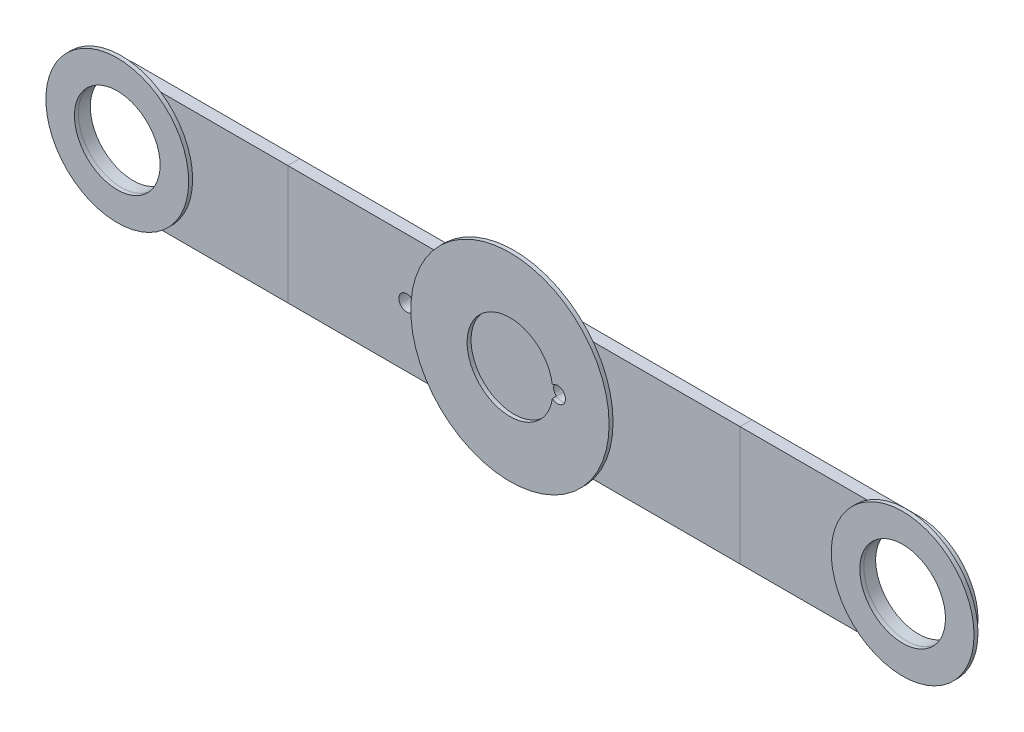
SolidWorks part; units mm, degrees
ref_plane "Front Plane" through (0, 0, 0) normal (0, 0, 1) x (1, 0, 0)
ref_plane "Top Plane" through (0, 0, 0) normal (0, 1, 0) x (1, 0, 0)
ref_plane "Right Plane" through (0, 0, 0) normal (1, 0, 0) x (0, 0, -1)
sketch "Sketch1" plane through (0, 0, 0) normal (0, 0, 1) x (1, 0, 0)
  line L0 (28.5, 7.5) -> (49.5, 7.5)
  line L1 (-28.5, -7.5) -> (28.5, -7.5)
  line L2 (-28.5, -7.5) -> (-28.5, 7.5)
  line L3 (-28.5, 7.5) -> (28.5, 7.5)
  line L4 (28.5, -7.5) -> (28.5, 7.5)
  line L5 (-28.5, -7.5) -> (28.5, 7.5) construction
  line L6 (-28.5, 7.5) -> (28.5, -7.5) construction
  line L7 (-49.5, -7.5) -> (-28.5, -7.5)
  line L8 (49.5, -7.5) -> (28.5, -7.5)
  line L9 (0, 7.5) -> (0, -7.5) construction
  line L10 (-28.5, 0) -> (28.5, 0) construction
  line L11 (-28.5, 7.5) -> (-49.5, 7.5)
  arc A0 (49.5, -7.5) -> (49.5, 7.5) centre (49.5, 0) ccw
  circle A1 centre (-49.5, 0) radius 5.4
  circle A2 centre (49.5, 0) radius 5.4
  arc A3 (-49.5, -7.5) -> (-49.5, 7.5) centre (-49.5, 0) cw
  point P0 (0, 0)
  point P18 (0, 0)
  dimension "D3" = 57
  dimension "D8" = 10.8
  dimension "D1" = 15
  dimension "D2" = 57
extrude "Boss-Extrude1" add sketch "Sketch1" along normal blind 1.5 contours A3 L7 L2 L11 A1 | L8 A0 L0 L4 A2
sketch "Sketch2" plane through (0, 0, 1.5) normal (0, 0, 1) x (1, 0, 0)
  line L1 (-28.5, -7.5) -> (28.5, -7.5)
  line L2 (-28.5, -7.5) -> (-28.5, 7.5)
  line L3 (-28.5, 7.5) -> (28.5, 7.5)
  line L4 (28.5, -7.5) -> (28.5, 7.5)
  line L5 (-28.5, -7.5) -> (28.5, 7.5) construction
  line L6 (-28.5, 7.5) -> (28.5, -7.5) construction
  circle A0 centre (0, 0) radius 5.4
  point P0 (0, 0)
  dimension "D1" = 10.8
extrude "Boss-Extrude2" add sketch "Sketch2" against normal blind 1.5 separate body
sketch "Sketch3" plane through (0, 0, 1.5) normal (0, 0, 1) x (1, 0, 0)
  circle A0 centre (0, 0) radius 12.5
  circle A1 centre (49.5, 0) radius 9
  circle A2 centre (-49.5, 0) radius 9
  circle A3 centre (49.5, 0) radius 5.4
  circle A4 centre (0, 0) radius 5.4
  circle A5 centre (-49.5, 0) radius 5.4
  dimension "D1" = 25
  dimension "D2" = 18
  dimension "D3" = 18
extrude "Boss-Extrude3" add sketch "Sketch3" along normal blind 0.5 separate body
sketch "Sketch4" plane through (0, 0, 1.5) normal (0, 0, 1) x (1, 0, 0)
  circle A0 centre (0, 0) radius 5.4
extrude "Boss-Extrude4" add sketch "Sketch4" against normal blind 1.5 separate body
sketch "Sketch5" plane through (0, 0, 1.5) normal (0, 0, 1) x (1, 0, 0)
  line L0 (-28.5, -7.5) -> (-28.5, 7.5) construction
  circle A0 centre (-13.5, 0) radius 1
  circle A1 centre (6, 0) radius 1
  dimension "D1" = 15
  dimension "D3" = 2
  dimension "D4" = 2
  dimension "D2" = 19.5
extrude "Cut-Extrude1" cut sketch "Sketch5" against normal through all both and the other way through all
